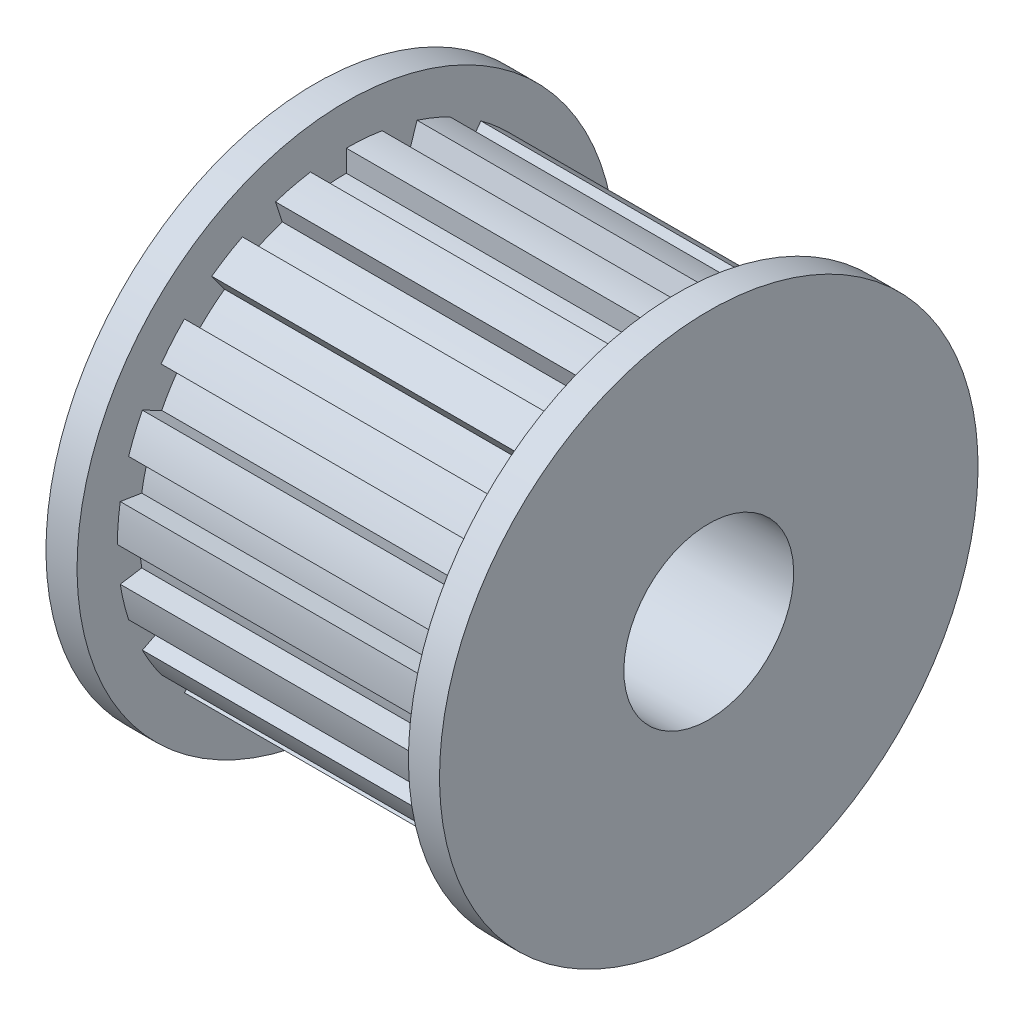
SolidWorks part; units mm, degrees
ref_plane "前视基准面" through (0, 0, 0) normal (0, 0, 1) x (1, 0, 0)
ref_plane "上视基准面" through (0, 0, 0) normal (0, 1, 0) x (1, 0, 0)
ref_plane "右视基准面" through (0, 0, 0) normal (1, 0, 0) x (0, 0, -1)
sketch "草图1" plane through (0, 0, 0) normal (0, 0, 1) x (1, 0, 0)
  line L0 (-9.5, 0) -> (9.5, 0)
  line L1 (9.5, 0) -> (9.5, 13)
  line L2 (9.5, 13) -> (8, 13)
  line L3 (8, 13) -> (8, 11.05)
  line L4 (8, 11.05) -> (-8, 11.05)
  line L5 (-8, 11.05) -> (-8, 13)
  line L6 (-8, 13) -> (-9.5, 13)
  line L7 (-9.5, 13) -> (-9.5, 0)
  line L8 (0, 27.7502) -> (0, -16.4737) construction
  dimension "D1" = 11.05
  dimension "D2" = 13
  dimension "D3" = 19
  dimension "D4" = 16
revolve "旋转1" add sketch "草图1" angle 360 about L0
sketch "草图2" plane through (0, 0, 0) normal (1, 0, 0) x (0, 0, -1)
  line L0 (-19.5115, 0) -> (20.7995, 0) construction
  line L1 (11.05, 0) -> (10, 0)
  line L2 (-34.9192, -5.5307) -> (34.9192, 5.5307) construction
  line L3 (10.914, 1.7286) -> (9.8769, 1.5643)
  line L4 (10.5092, -3.4146) -> (9.5106, -3.0902)
  line L5 (10.914, -1.7286) -> (9.8769, -1.5643)
  line L6 (8.9396, -6.495) -> (8.0902, -5.8779)
  line L7 (9.8456, -5.0166) -> (8.9101, -4.5399)
  line L8 (6.495, -8.9396) -> (5.8779, -8.0902)
  line L9 (7.8135, -7.8135) -> (7.0711, -7.0711)
  line L10 (3.4146, -10.5092) -> (3.0902, -9.5106)
  line L11 (5.0166, -9.8456) -> (4.5399, -8.9101)
  line L12 (0, -11.05) -> (0, -10)
  line L13 (1.7286, -10.914) -> (1.5643, -9.8769)
  line L14 (-3.4146, -10.5092) -> (-3.0902, -9.5106)
  line L15 (-1.7286, -10.914) -> (-1.5643, -9.8769)
  line L16 (-6.495, -8.9396) -> (-5.8779, -8.0902)
  line L17 (-5.0166, -9.8456) -> (-4.5399, -8.9101)
  line L18 (-8.9396, -6.495) -> (-8.0902, -5.8779)
  line L19 (-7.8135, -7.8135) -> (-7.0711, -7.0711)
  line L20 (-10.5092, -3.4146) -> (-9.5106, -3.0902)
  line L21 (-9.8456, -5.0166) -> (-8.9101, -4.5399)
  line L22 (-11.05, 0) -> (-10, 0)
  line L23 (-10.914, -1.7286) -> (-9.8769, -1.5643)
  line L24 (-10.5092, 3.4146) -> (-9.5106, 3.0902)
  line L25 (-10.914, 1.7286) -> (-9.8769, 1.5643)
  line L26 (-8.9396, 6.495) -> (-8.0902, 5.8779)
  line L27 (-9.8456, 5.0166) -> (-8.9101, 4.5399)
  line L28 (-6.495, 8.9396) -> (-5.8779, 8.0902)
  line L29 (-7.8135, 7.8135) -> (-7.0711, 7.0711)
  line L30 (-3.4146, 10.5092) -> (-3.0902, 9.5106)
  line L31 (-5.0166, 9.8456) -> (-4.5399, 8.9101)
  line L32 (0, 11.05) -> (0, 10)
  line L33 (-1.7286, 10.914) -> (-1.5643, 9.8769)
  line L34 (3.4146, 10.5092) -> (3.0902, 9.5106)
  line L35 (1.7286, 10.914) -> (1.5643, 9.8769)
  line L36 (6.495, 8.9396) -> (5.8779, 8.0902)
  line L37 (5.0166, 9.8456) -> (4.5399, 8.9101)
  line L38 (8.9396, 6.495) -> (8.0902, 5.8779)
  line L39 (7.8135, 7.8135) -> (7.0711, 7.0711)
  line L40 (10.5092, 3.4146) -> (9.5106, 3.0902)
  line L41 (9.8456, 5.0166) -> (8.9101, 4.5399)
  arc A0 (11.05, 0) -> (10.914, 1.7286) centre (0, 0) ccw
  arc A2 (10, 0) -> (9.8769, 1.5643) centre (0, 0) ccw
  arc A3 (10.5092, -3.4146) -> (10.914, -1.7286) centre (0, 0) ccw
  arc A4 (9.5106, -3.0902) -> (9.8769, -1.5643) centre (0, 0) ccw
  arc A5 (8.9396, -6.495) -> (9.8456, -5.0166) centre (0, 0) ccw
  arc A6 (8.0902, -5.8779) -> (8.9101, -4.5399) centre (0, 0) ccw
  arc A7 (6.495, -8.9396) -> (7.8135, -7.8135) centre (0, 0) ccw
  arc A8 (5.8779, -8.0902) -> (7.0711, -7.0711) centre (0, 0) ccw
  arc A9 (3.4146, -10.5092) -> (5.0166, -9.8456) centre (0, 0) ccw
  arc A10 (3.0902, -9.5106) -> (4.5399, -8.9101) centre (0, 0) ccw
  arc A11 (0, -11.05) -> (1.7286, -10.914) centre (0, 0) ccw
  arc A12 (0, -10) -> (1.5643, -9.8769) centre (0, 0) ccw
  arc A13 (-3.4146, -10.5092) -> (-1.7286, -10.914) centre (0, 0) ccw
  arc A14 (-3.0902, -9.5106) -> (-1.5643, -9.8769) centre (0, 0) ccw
  arc A15 (-6.495, -8.9396) -> (-5.0166, -9.8456) centre (0, 0) ccw
  arc A16 (-5.8779, -8.0902) -> (-4.5399, -8.9101) centre (0, 0) ccw
  arc A17 (-8.9396, -6.495) -> (-7.8135, -7.8135) centre (0, 0) ccw
  arc A18 (-8.0902, -5.8779) -> (-7.0711, -7.0711) centre (0, 0) ccw
  arc A19 (-10.5092, -3.4146) -> (-9.8456, -5.0166) centre (0, 0) ccw
  arc A20 (-9.5106, -3.0902) -> (-8.9101, -4.5399) centre (0, 0) ccw
  arc A21 (-11.05, 0) -> (-10.914, -1.7286) centre (0, 0) ccw
  arc A22 (-10, 0) -> (-9.8769, -1.5643) centre (0, 0) ccw
  arc A23 (-10.5092, 3.4146) -> (-10.914, 1.7286) centre (0, 0) ccw
  arc A24 (-9.5106, 3.0902) -> (-9.8769, 1.5643) centre (0, 0) ccw
  arc A25 (-8.9396, 6.495) -> (-9.8456, 5.0166) centre (0, 0) ccw
  arc A26 (-8.0902, 5.8779) -> (-8.9101, 4.5399) centre (0, 0) ccw
  arc A27 (-6.495, 8.9396) -> (-7.8135, 7.8135) centre (0, 0) ccw
  arc A28 (-5.8779, 8.0902) -> (-7.0711, 7.0711) centre (0, 0) ccw
  arc A29 (-3.4146, 10.5092) -> (-5.0166, 9.8456) centre (0, 0) ccw
  arc A30 (-3.0902, 9.5106) -> (-4.5399, 8.9101) centre (0, 0) ccw
  arc A31 (0, 11.05) -> (-1.7286, 10.914) centre (0, 0) ccw
  arc A32 (0, 10) -> (-1.5643, 9.8769) centre (0, 0) ccw
  arc A33 (3.4146, 10.5092) -> (1.7286, 10.914) centre (0, 0) ccw
  arc A34 (3.0902, 9.5106) -> (1.5643, 9.8769) centre (0, 0) ccw
  arc A35 (6.495, 8.9396) -> (5.0166, 9.8456) centre (0, 0) ccw
  arc A36 (5.8779, 8.0902) -> (4.5399, 8.9101) centre (0, 0) ccw
  arc A37 (8.9396, 6.495) -> (7.8135, 7.8135) centre (0, 0) ccw
  arc A38 (8.0902, 5.8779) -> (7.0711, 7.0711) centre (0, 0) ccw
  arc A39 (10.5092, 3.4146) -> (9.8456, 5.0166) centre (0, 0) ccw
  arc A40 (9.5106, 3.0902) -> (8.9101, 4.5399) centre (0, 0) ccw
  point P88 (0, 0)
  dimension "D1" = 22.1
  dimension "D2" = 20
  dimension "D4" = 10
  dimension "D3" = 9
extrude "切除-拉伸1" cut sketch "草图2" against normal mid plane 16
sketch "草图7" plane through (0, 0, 0) normal (1, 0, 0) x (0, 0, -1)
  circle A0 centre (0, 0) radius 4.1
  dimension "D1" = 8.2
extrude "切除-拉伸3" cut sketch "草图7" against normal mid plane 20
